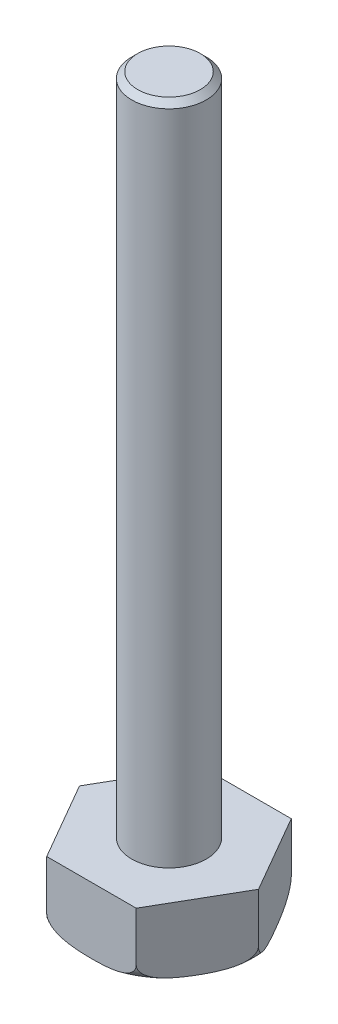
SolidWorks part; units mm, degrees
ref_plane "Front Plane" through (0, 0, 0) normal (0, 0, 1) x (1, 0, 0)
ref_plane "Top Plane" through (0, 0, 0) normal (0, 1, 0) x (1, 0, 0)
ref_plane "Right Plane" through (0, 0, 0) normal (1, 0, 0) x (0, 0, -1)
sketch "Sketch1" plane through (0, 0, 0) normal (0, 1, 0) x (1, 0, 0)
  line L1 (-60.0444, 0) -> (-30.0222, -52)
  line L2 (-30.0222, -52) -> (30.0222, -52)
  line L3 (30.0222, -52) -> (60.0444, 0)
  line L4 (60.0444, 0) -> (30.0222, 52)
  line L5 (30.0222, 52) -> (-30.0222, 52)
  line L6 (-30.0222, 52) -> (-60.0444, 0)
  circle A0 centre (0, 0) radius 52 construction
  dimension "D1" = 104
extrude "Boss-Extrude1" add sketch "Sketch1" along normal blind 45
sketch "Sketch2" plane through (0, 45, 0) normal (0, 1, 0) x (1, 0, 0)
  circle A0 centre (0, 0) radius 25
  dimension "D1" = 50
extrude "Boss-Extrude2" add sketch "Sketch2" along normal blind 445
sketch "Sketch3" plane through (0, 0, 0) normal (0, 0, 1) x (1, 0, 0)
  line L0 (30.0222, 0) -> (60.0444, 0) construction
  line L1 (60.0444, 45) -> (60.0444, 0) construction
  line L2 (48.0444, 0) -> (60.0444, 0)
  line L3 (60.0444, 0) -> (60.0444, 12)
  arc A0 (48.0444, 0) -> (60.0444, 12) centre (48.0444, 12) ccw
  dimension "D1" = 12
revolve "Cut-Revolve1" cut sketch "Sketch3" angle 360 about axis through (0, 490, 0) along (0, -1, 0)
chamfer "Chamfer1" distance 4 angle 45 1 edges at (0, 490, 25)
